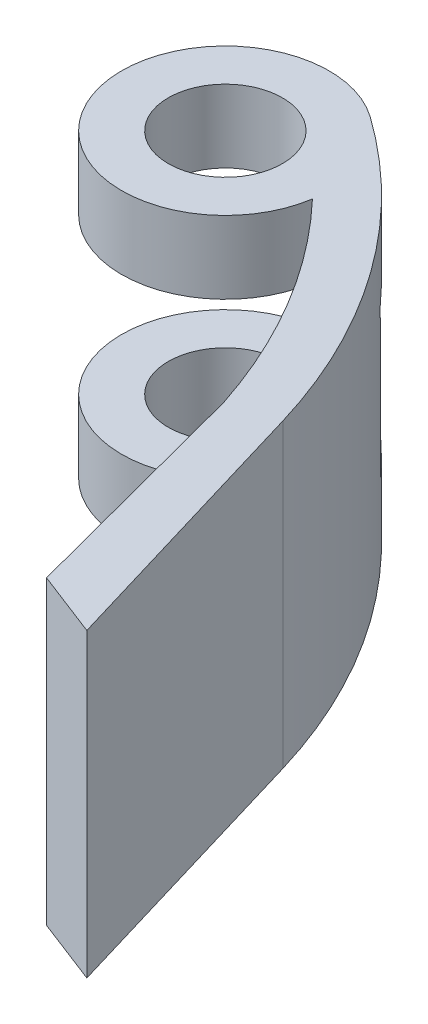
SolidWorks part; units mm, degrees
material "Plain Carbon Steel"
ref_plane "Front Plane" through (0, 0, 0) normal (0, 0, 1) x (1, 0, 0)
ref_plane "Top Plane" through (0, 0, 0) normal (0, 1, 0) x (1, 0, 0)
ref_plane "Right Plane" through (0, 0, 0) normal (1, 0, 0) x (0, 0, -1)
sketch "Sketch2" plane through (0, 0, 0) normal (0, 1, 0) x (1, 0, 0)
  line L0 (28.8185, 70.9167) -> (26.2959, 67.1881)
  line L1 (50.0098, 41.3112) -> (58.0453, 14.3988)
  line L2 (50.0098, 41.3112) -> (45.6189, 40.0002)
  line L3 (45.6189, 40.0002) -> (51.7108, 16.8486)
  line L4 (51.7108, 16.8486) -> (58.0453, 14.3988)
  arc A0 (45.6189, 40.0002) -> (26.2959, 67.1881) centre (-7.6173, 22.6247) ccw
  arc A2 (50.0098, 41.3112) -> (28.8185, 70.9167) centre (-3.6494, 25.2896) ccw
  circle A3 centre (23.0207, 62.769) radius 10
  circle A4 centre (23.0207, 62.769) radius 5.5
extrude "Boss-Extrude1" add sketch "Sketch2" along normal blind 29 contours A0 A4 L0 A3 | A0 A3 L0 | A3 A0 L2 A2 | L3 L4 L1 L2
ref_plane "Plane1" through (0, 7, 0) normal (0, -1, 0) x (-1, 0, 0)
sketch "Sketch3" plane through (0, 7, 0) normal (0, -1, 0) x (-1, 0, 0)
  line L0 (-39.7728, 64.267) -> (-15.8938, 42.0423)
  line L1 (-39.7728, 64.267) -> (-23.9402, 82.938)
  line L2 (-15.8938, 42.0423) -> (-0.0612, 60.7132)
  line L3 (-23.9402, 82.938) -> (-0.0612, 60.7132)
  circle A0 centre (-23.0207, 62.769) radius 12
extrude "Cut-Extrude2" cut sketch "Sketch3" against normal blind 14 contours A0 L0 L2 L3 L1 | L0 A0 | L0 A0
ref_plane "Plane2" through (52.5086, 0, -13.8167) normal (-0.9671, 0, 0.2545) x (0.2545, 0, 0.9671)
ref_plane "Plane3" through (0, 14.5, 0) normal (0, -1, 0) x (-1, 0, 0)
sketch "Sketch5" plane through (0, 14.5, 0) normal (0, -1, 0) x (-1, 0, 0)
  line L0 (-45.6189, 40.0002) -> (-52.0035, 15.7361) construction
  circle A0 centre (-48.8112, 27.8681) radius 2
  circle A1 centre (-48.8112, 27.8681) radius 4
extrude "Boss-Extrude2" add sketch "Sketch5" along normal blind 1 and the other way blind 1
ref_plane "Plane4" through (0, 22, 0) normal (0, 1, 0) x (1, 0, 0)
sketch "Sketch6" plane through (0, 22, 0) normal (0, 1, 0) x (1, 0, 0)
  line L0 (39.539, 63.8318) -> (17.0179, 43.8597)
  line L1 (39.539, 63.8318) -> (24.4096, 83.6193)
  line L2 (17.0179, 43.8597) -> (2.6673, 64.3378)
  line L3 (24.4096, 83.6193) -> (2.6673, 64.3378)
  circle A0 centre (23.0207, 62.769) radius 12
extrude "Cut-Extrude3" cut sketch "Sketch6" against normal blind 1 contours A0 L0 L1 L3 L2 | L0 A0 | L0 A0
